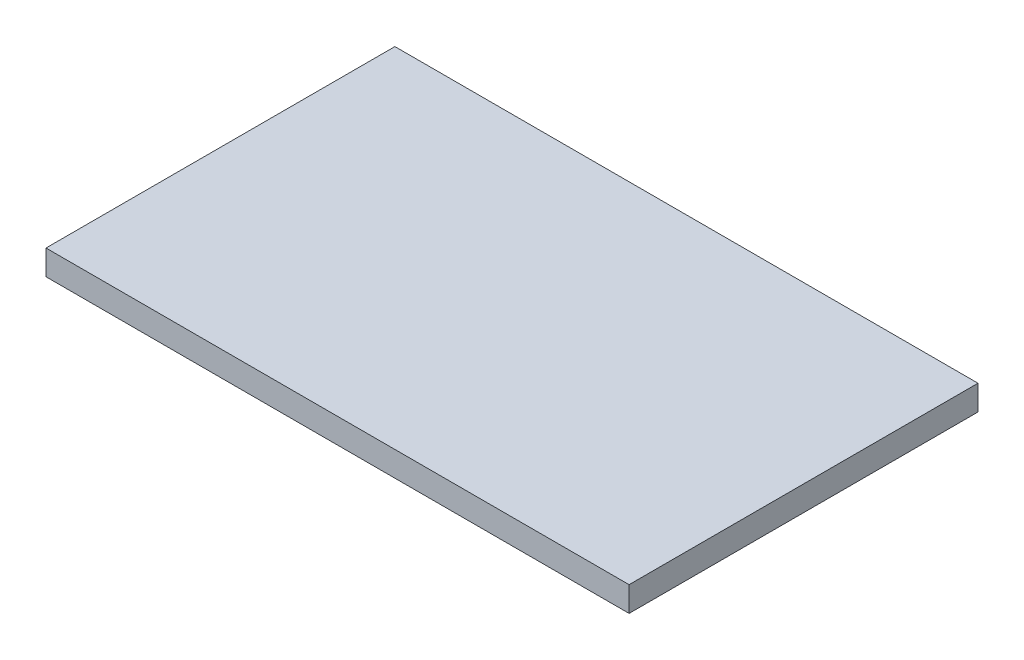
SolidWorks part; units mm, degrees
ref_plane "Front Plane" through (0, 0, 0) normal (0, 0, 1) x (1, 0, 0)
ref_plane "Top Plane" through (0, 0, 0) normal (0, 1, 0) x (1, 0, 0)
ref_plane "Right Plane" through (0, 0, 0) normal (1, 0, 0) x (0, 0, -1)
sketch "Sketch1" plane through (0, 0, 0) normal (0, 1, 0) x (1, 0, 0)
  line L1 (0, 0) -> (36.5, 0)
  line L2 (0, 0) -> (0, 21.84)
  line L3 (0, 21.84) -> (36.5, 21.84)
  line L4 (36.5, 0) -> (36.5, 21.84)
  dimension "D1" = 36.5
  dimension "D2" = 21.84
extrude "Boss-Extrude1" add sketch "Sketch1" along normal blind 1.56 contours L2 L3 L4 L1
